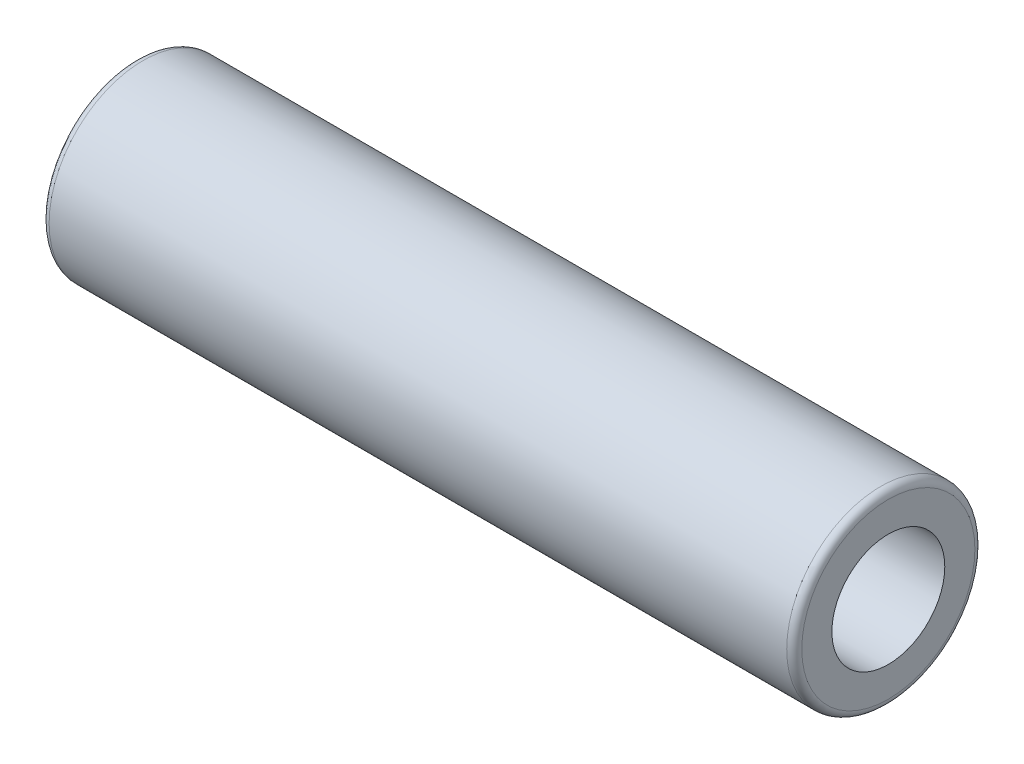
SolidWorks part; units mm, degrees
ref_plane "Front Plane" through (0, 0, 0) normal (0, 0, 1) x (1, 0, 0)
ref_plane "Top Plane" through (0, 0, 0) normal (0, 1, 0) x (1, 0, 0)
ref_plane "Right Plane" through (0, 0, 0) normal (1, 0, 0) x (0, 0, -1)
sketch "Sketch1" plane through (0, 0, 0) normal (1, 0, 0) x (0, 0, -1)
  circle A1 centre (0, 0) radius 6.25
  circle A2 centre (0, 0) radius 3.75
  circle A3 centre (0, 0) radius 6.25
  dimension "D1" = 12.5
  dimension "D2" = 7.5
extrude "Boss-Extrude2" add sketch "Sketch1" along normal blind 50 contours A1 A2
fillet "Fillet1" radius 0.5 1 edges at (0, 0, -6.25)
fillet "Fillet2" radius 0.5 1 edges at (50, 0, -6.25)
